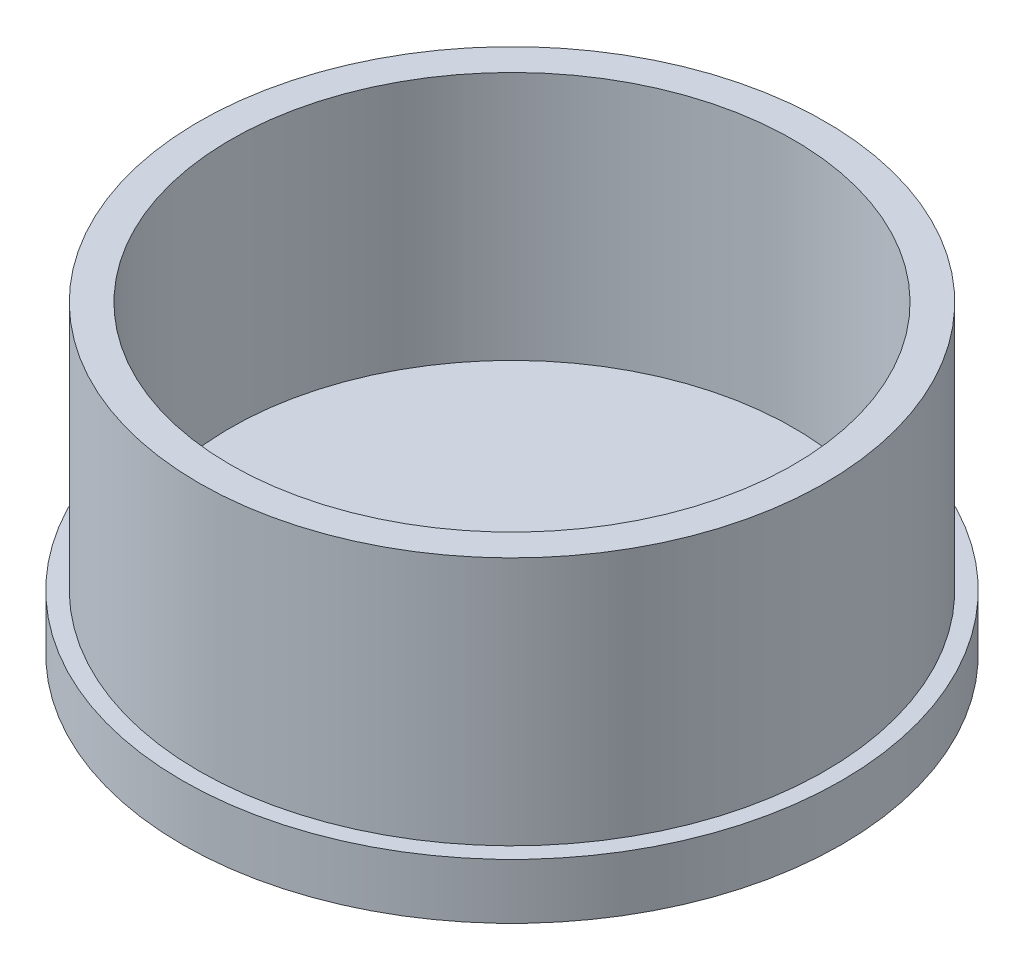
SolidWorks part; units mm, degrees
ref_plane "Plano frontal" through (0, 0, 0) normal (0, 0, 1) x (1, 0, 0)
ref_plane "Plano superior" through (0, 0, 0) normal (0, 1, 0) x (1, 0, 0)
ref_plane "Plano direito" through (0, 0, 0) normal (1, 0, 0) x (0, 0, -1)
sketch "Esboço1" plane through (0, 0, 0) normal (0, 1, 0) x (1, 0, 0)
  circle A0 centre (0, 0) radius 59.5
extrude "Ressalto-extrusão1" add sketch "Esboço1" along normal blind 55
sketch "Esboço2" plane through (0, 55, 0) normal (0, 1, 0) x (1, 0, 0)
  circle A0 centre (0, 0) radius 50.8
extrude "Corte-extrusão1" cut sketch "Esboço2" against normal blind 45
sketch "Esboço3" plane through (0, 55, 0) normal (0, 1, 0) x (1, 0, 0)
  circle A0 centre (0, 0) radius 59.5
  circle A1 centre (0, 0) radius 56.5
extrude "Corte-extrusão2" cut sketch "Esboço3" against normal blind 45
